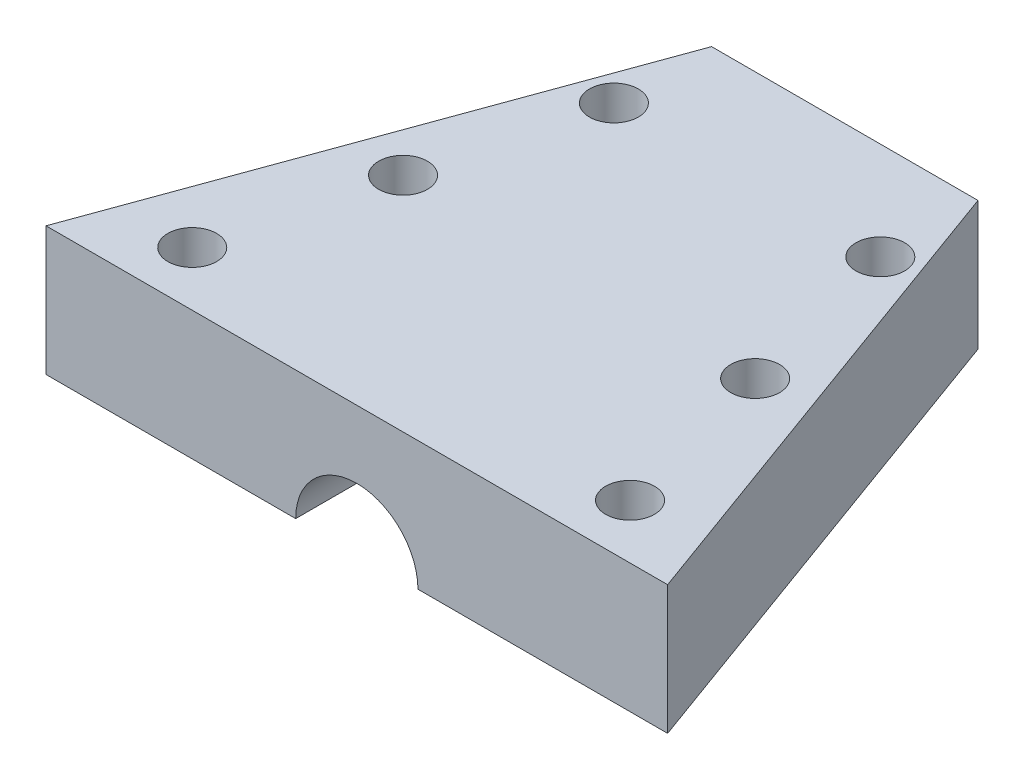
SolidWorks part; units mm, degrees
ref_plane "Front Plane" through (0, 0, 0) normal (0, 0, 1) x (1, 0, 0)
ref_plane "Top Plane" through (0, 0, 0) normal (0, 1, 0) x (1, 0, 0)
ref_plane "Right Plane" through (0, 0, 0) normal (1, 0, 0) x (0, 0, -1)
sketch "Sketch6" plane through (0, 0, 0) normal (0, 1, 0) x (1, 0, 0)
  line L0 (-16.8369, 5.7834) -> (13.1631, 5.7834)
  line L1 (13.1631, 5.7834) -> (33.1631, -49.1662)
  line L2 (33.1631, -49.1662) -> (-36.8369, -49.1662)
  line L3 (-36.8369, -49.1662) -> (-16.8369, 5.7834)
  circle A0 centre (13.1631, -5.2166) radius 1.78
  circle A1 centre (-16.8369, -5.2166) radius 1.78
  circle A2 centre (-26.4869, -43.0491) radius 1.78
  circle A3 centre (22.8131, -43.0491) radius 1.78
  dimension "D1" = 3.56
  dimension "D3" = 3.56
  dimension "D4" = 3.56
  dimension "D5" = 3.56
  dimension "D2" = 70
  dimension "D6" = 30
  dimension "D7" = 11
  dimension "D8" = 11
  dimension "D9" = 49.3
  dimension "D10" = 10.35
  dimension "D11" = 10.35
  dimension "D12" = 30
extrude "Boss-Extrude3" add sketch "Sketch6" along normal blind 14.5 contours L3 L0 L1 L2
sketch "Sketch8" plane through (0, 0, 49.1662) normal (0, 0, 1) x (1, 0, 0)
  line L0 (33.1631, 0) -> (-36.8369, 0) construction
  circle A0 centre (-1.8369, 0) radius 6.8846
extrude "Cut-Extrude3" cut sketch "Sketch8" against normal blind 88
sketch "Sketch9" plane through (0, 14.5, 0) normal (0, 1, 0) x (1, 0, 0)
  point P0 (-16.8369, -5.2166)
  point P1 (13.1631, -5.2166)
  point P3 (22.8131, -43.0491)
  point P5 (-26.4869, -43.0491)
  point P7 (17.9881, -24.1329)
  point P9 (-21.6619, -24.1329)
hole_wizard "#39 (0.21653543) Diameter Hole1" positions "3DSketch2" profile "Sketch11" hole size "#39" standard "ANSI Inch" end condition through all
sketch3d "3DSketch2"
  point P0 (-16.8369, 0, 5.2166)
  point P3 (13.1631, 0, 5.2166)
  point P6 (22.8131, 0, 43.0491)
  point P9 (-26.4869, 0, 43.0491)
  point P13 (22.8131, 14.5, 43.0491)
  point P16 (-26.4869, 14.5, 43.0491)
  point P19 (-16.8369, 14.5, 5.2166)
  point P22 (13.1631, 14.5, 5.2166)
  point P25 (-21.6619, 14.5, 24.1329)
  point P28 (17.9881, 14.5, 24.1329)
sketch "Sketch11" plane through (17.9881, 14.5, 24.1329) normal (1, 0, 0) x (0, 0, 1)
  line L0 (0, 0) -> (0, 14.5)
  line L1 (0, 14.5) -> (2.75, 14.5)
  line L2 (2.75, 14.5) -> (2.75, 0)
  line L5 (2.75, 0) -> (0, 0)
  line L11 (0, -6.35) -> (0, 107.95) construction
  dimension "Thru Hole Dia." = 5.5
  dimension "Thru Hole Depth" = 14.5
